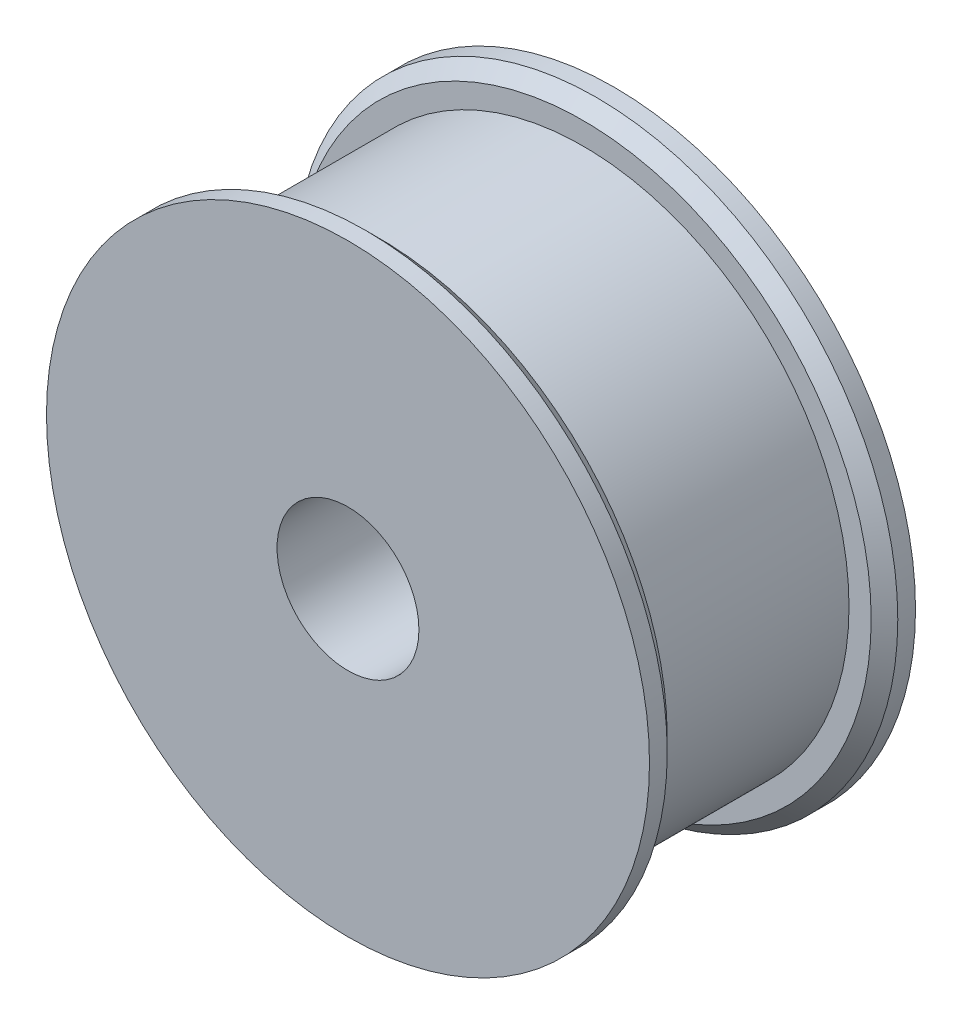
SolidWorks part; units mm, degrees
material "3.0255 (EN-AW 1350A)"
ref_plane "Plan de face" through (0, 0, 0) normal (0, 0, 1) x (1, 0, 0)
ref_plane "Plan de dessus" through (0, 0, 0) normal (0, 1, 0) x (1, 0, 0)
ref_plane "Plan de droite" through (0, 0, 0) normal (1, 0, 0) x (0, 0, -1)
sketch "Esquisse1" plane through (0, 0, 0) normal (1, 0, 0) x (0, 0, -1)
  line L0 (-15, 0) -> (0, 0)
  line L2 (0, 0) -> (0, 17)
  line L3 (0, 17) -> (-15, 17)
  line L4 (-15, 0) -> (-15, 17)
  line L5 (0, 0) -> (-15, 17) construction
  line L6 (0, 17) -> (0, 0) construction
  line L7 (-15, 0) -> (0, 0)
  line L8 (-15, 0) -> (-15, 15)
  line L9 (-15, 15) -> (0, 15)
  line L10 (0, 0) -> (0, 15)
  line L11 (-15, 0) -> (0, 0)
  line L12 (-15, 0) -> (-15, 11)
  line L13 (-15, 11) -> (0, 11)
  line L14 (0, 0) -> (0, 11)
  line L15 (-15, 15) -> (-13.25, 15)
  line L16 (-15, 15) -> (-15, 17)
  line L17 (-15, 17) -> (-13.25, 17)
  line L18 (-13.25, 15) -> (-13.25, 17)
  line L19 (0, 15) -> (-1.75, 15)
  line L20 (0, 15) -> (0, 17)
  line L21 (0, 17) -> (-1.75, 17)
  line L22 (-1.75, 15) -> (-1.75, 17)
  line L23 (-15, 11) -> (0, 11)
  line L24 (-15, 11) -> (-15, 4)
  line L25 (-15, 4) -> (0, 4)
  line L26 (0, 11) -> (0, 4)
  point P0 (0, 0)
  dimension "D1" = 15
  dimension "D2" = 17
  dimension "D3" = 15
  dimension "D4" = 11
  dimension "D5" = 1.75
  dimension "D6" = 1.75
  dimension "D7" = 7
revolve "Révolution1" add sketch "Esquisse1" angle 360 about L0
chamfer "Chanfrein1" distance 0.75 angle 45 2 edges at (17, 0, 1.75) (17, 0, 13.25)
